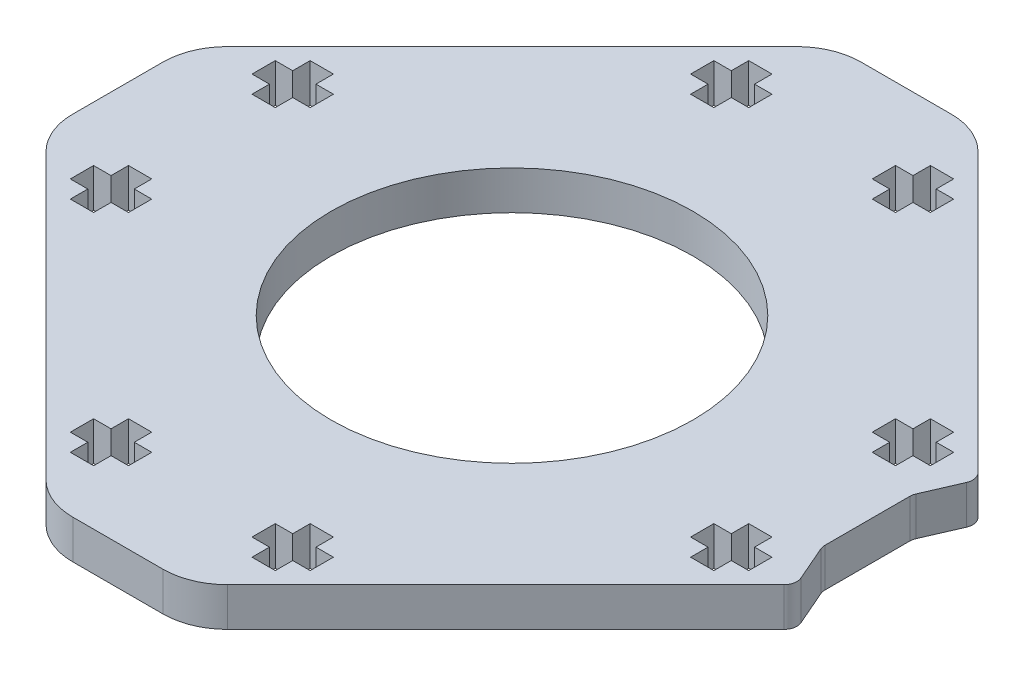
SolidWorks part; units mm, degrees
ref_plane "Front Plane" through (0, 0, 0) normal (0, 0, 1) x (1, 0, 0)
ref_plane "Top Plane" through (0, 0, 0) normal (0, 1, 0) x (1, 0, 0)
ref_plane "Right Plane" through (0, 0, 0) normal (1, 0, 0) x (0, 0, -1)
sketch "Sketch1" plane through (0, 0, 0) normal (0, 1, 0) x (1, 0, 0)
  line L0 (3.4914, 30.5) -> (-3.4914, 30.5)
  line L1 (-7.0269, 29.0355) -> (-29.0355, 7.0269)
  line L2 (-30.5, 3.4914) -> (-30.5, -3.4914)
  line L3 (-29.0355, -7.0269) -> (-7.0269, -29.0355)
  line L4 (-3.4914, -30.5) -> (3.4914, -30.5)
  line L5 (7.0269, -29.0355) -> (29.0355, -7.0269)
  line L7 (29.0355, 7.0269) -> (7.0269, 29.0355)
  line L9 (27.5, 3.4914) -> (27.5, -3.4914)
  line L11 (29.0355, 7.0269) -> (27.5, 3.4914)
  line L12 (27.5, -3.4914) -> (29.0355, -7.0269)
  arc A0 (7.0269, 29.0355) -> (3.4914, 30.5) centre (3.4914, 25.5) ccw
  arc A1 (-3.4914, 30.5) -> (-7.0269, 29.0355) centre (-3.4914, 25.5) ccw
  arc A2 (-29.0355, 7.0269) -> (-30.5, 3.4914) centre (-25.5, 3.4914) ccw
  arc A3 (-30.5, -3.4914) -> (-29.0355, -7.0269) centre (-25.5, -3.4914) ccw
  arc A4 (-7.0269, -29.0355) -> (-3.4914, -30.5) centre (-3.4914, -25.5) ccw
  arc A5 (3.4914, -30.5) -> (7.0269, -29.0355) centre (3.4914, -25.5) ccw
  circle A16 centre (0, 0) radius 14
  dimension "D1" = 28
  dimension "D2" = 31.1249
  dimension "D3" = 51
extrude "Boss-Extrude1" add sketch "Sketch1" along normal blind 3
sketch "Sketch2" plane through (0, 3, 0) normal (0, 1, 0) x (1, 0, 0)
  line L12 (-26.25, 7.9294) -> (-26.25, 6.1294)
  line L13 (-26.25, 6.1294) -> (-24.9, 6.1294)
  line L14 (-24.9, 6.1294) -> (-24.9, 4.7794)
  line L15 (-24.9, 4.7794) -> (-23.1, 4.7794)
  line L16 (-23.1, 4.7794) -> (-23.1, 6.1294)
  line L17 (-23.1, 6.1294) -> (-21.75, 6.1294)
  line L18 (-21.75, 6.1294) -> (-21.75, 7.9294)
  line L19 (-21.75, 7.9294) -> (-23.1, 7.9294)
  line L20 (-23.1, 7.9294) -> (-23.1, 9.2794)
  line L21 (-23.1, 9.2794) -> (-24.9, 9.2794)
  line L22 (-24.9, 9.2794) -> (-24.9, 7.9294)
  line L23 (-24.9, 7.9294) -> (-26.25, 7.9294)
  line L24 (-26.25, 7.9294) -> (-26.25, 6.1294)
  line L25 (-26.25, 6.1294) -> (-24.9, 6.1294)
  line L26 (-24.9, 6.1294) -> (-24.9, 4.7794)
  line L27 (-24.9, 4.7794) -> (-23.1, 4.7794)
  line L28 (-23.1, 4.7794) -> (-23.1, 6.1294)
  line L29 (-23.1, 6.1294) -> (-21.75, 6.1294)
  line L30 (-21.75, 6.1294) -> (-21.75, 7.9294)
  line L31 (-21.75, 7.9294) -> (-23.1, 7.9294)
  line L32 (-23.1, 7.9294) -> (-23.1, 9.2794)
  line L33 (-23.1, 9.2794) -> (-24.9, 9.2794)
  line L34 (-24.9, 9.2794) -> (-24.9, 7.9294)
  line L35 (-24.9, 7.9294) -> (-26.25, 7.9294)
  line L36 (-23.1, -4.7794) -> (-24.9, -4.7794)
  line L37 (-24.9, -4.7794) -> (-24.9, -6.1294)
  line L38 (-24.9, -6.1294) -> (-26.25, -6.1294)
  line L39 (-26.25, -6.1294) -> (-26.25, -7.9294)
  line L40 (-26.25, -7.9294) -> (-24.9, -7.9294)
  line L41 (-24.9, -7.9294) -> (-24.9, -9.2794)
  line L42 (-24.9, -9.2794) -> (-23.1, -9.2794)
  line L43 (-23.1, -9.2794) -> (-23.1, -7.9294)
  line L44 (-23.1, -7.9294) -> (-21.75, -7.9294)
  line L45 (-21.75, -7.9294) -> (-21.75, -6.1294)
  line L46 (-21.75, -6.1294) -> (-23.1, -6.1294)
  line L47 (-23.1, -6.1294) -> (-23.1, -4.7794)
  line L48 (-23.1, -4.7794) -> (-24.9, -4.7794)
  line L49 (-24.9, -4.7794) -> (-24.9, -6.1294)
  line L50 (-24.9, -6.1294) -> (-26.25, -6.1294)
  line L51 (-26.25, -6.1294) -> (-26.25, -7.9294)
  line L52 (-26.25, -7.9294) -> (-24.9, -7.9294)
  line L53 (-24.9, -7.9294) -> (-24.9, -9.2794)
  line L54 (-24.9, -9.2794) -> (-23.1, -9.2794)
  line L55 (-23.1, -9.2794) -> (-23.1, -7.9294)
  line L56 (-23.1, -7.9294) -> (-21.75, -7.9294)
  line L57 (-21.75, -7.9294) -> (-21.75, -6.1294)
  line L58 (-21.75, -6.1294) -> (-23.1, -6.1294)
  line L59 (-23.1, -6.1294) -> (-23.1, -4.7794)
  line L60 (7.9294, 23.1) -> (9.2794, 23.1)
  line L61 (9.2794, 23.1) -> (9.2794, 24.9)
  line L62 (9.2794, 24.9) -> (7.9294, 24.9)
  line L63 (7.9294, 24.9) -> (7.9294, 26.25)
  line L64 (7.9294, 26.25) -> (6.1294, 26.25)
  line L65 (6.1294, 26.25) -> (6.1294, 24.9)
  line L66 (6.1294, 24.9) -> (4.7794, 24.9)
  line L67 (4.7794, 24.9) -> (4.7794, 23.1)
  line L68 (4.7794, 23.1) -> (6.1294, 23.1)
  line L69 (6.1294, 23.1) -> (6.1294, 21.75)
  line L70 (6.1294, 21.75) -> (7.9294, 21.75)
  line L71 (7.9294, 21.75) -> (7.9294, 23.1)
  line L72 (7.9294, 23.1) -> (9.2794, 23.1)
  line L73 (9.2794, 23.1) -> (9.2794, 24.9)
  line L74 (9.2794, 24.9) -> (7.9294, 24.9)
  line L75 (7.9294, 24.9) -> (7.9294, 26.25)
  line L76 (7.9294, 26.25) -> (6.1294, 26.25)
  line L77 (6.1294, 26.25) -> (6.1294, 24.9)
  line L78 (6.1294, 24.9) -> (4.7794, 24.9)
  line L79 (4.7794, 24.9) -> (4.7794, 23.1)
  line L80 (4.7794, 23.1) -> (6.1294, 23.1)
  line L81 (6.1294, 23.1) -> (6.1294, 21.75)
  line L82 (6.1294, 21.75) -> (7.9294, 21.75)
  line L83 (7.9294, 21.75) -> (7.9294, 23.1)
  line L84 (26.25, -7.9294) -> (26.25, -6.1294)
  line L85 (26.25, -6.1294) -> (24.9, -6.1294)
  line L86 (24.9, -6.1294) -> (24.9, -4.7794)
  line L87 (24.9, -4.7794) -> (23.1, -4.7794)
  line L88 (23.1, -4.7794) -> (23.1, -6.1294)
  line L89 (23.1, -6.1294) -> (21.75, -6.1294)
  line L90 (21.75, -6.1294) -> (21.75, -7.9294)
  line L91 (21.75, -7.9294) -> (23.1, -7.9294)
  line L92 (23.1, -7.9294) -> (23.1, -9.2794)
  line L93 (23.1, -9.2794) -> (24.9, -9.2794)
  line L94 (24.9, -9.2794) -> (24.9, -7.9294)
  line L95 (24.9, -7.9294) -> (26.25, -7.9294)
  line L96 (26.25, -7.9294) -> (26.25, -6.1294)
  line L97 (26.25, -6.1294) -> (24.9, -6.1294)
  line L98 (24.9, -6.1294) -> (24.9, -4.7794)
  line L99 (24.9, -4.7794) -> (23.1, -4.7794)
  line L100 (23.1, -4.7794) -> (23.1, -6.1294)
  line L101 (23.1, -6.1294) -> (21.75, -6.1294)
  line L102 (21.75, -6.1294) -> (21.75, -7.9294)
  line L103 (21.75, -7.9294) -> (23.1, -7.9294)
  line L104 (23.1, -7.9294) -> (23.1, -9.2794)
  line L105 (23.1, -9.2794) -> (24.9, -9.2794)
  line L106 (24.9, -9.2794) -> (24.9, -7.9294)
  line L107 (24.9, -7.9294) -> (26.25, -7.9294)
  line L108 (-4.7794, 24.9) -> (-6.1294, 24.9)
  line L109 (-6.1294, 24.9) -> (-6.1294, 26.25)
  line L110 (-6.1294, 26.25) -> (-7.9294, 26.25)
  line L111 (-7.9294, 26.25) -> (-7.9294, 24.9)
  line L112 (-7.9294, 24.9) -> (-9.2794, 24.9)
  line L113 (-9.2794, 24.9) -> (-9.2794, 23.1)
  line L114 (-9.2794, 23.1) -> (-7.9294, 23.1)
  line L115 (-7.9294, 23.1) -> (-7.9294, 21.75)
  line L116 (-7.9294, 21.75) -> (-6.1294, 21.75)
  line L117 (-6.1294, 21.75) -> (-6.1294, 23.1)
  line L118 (-6.1294, 23.1) -> (-4.7794, 23.1)
  line L119 (-4.7794, 23.1) -> (-4.7794, 24.9)
  line L120 (-4.7794, 24.9) -> (-6.1294, 24.9)
  line L121 (-6.1294, 24.9) -> (-6.1294, 26.25)
  line L122 (-6.1294, 26.25) -> (-7.9294, 26.25)
  line L123 (-7.9294, 26.25) -> (-7.9294, 24.9)
  line L124 (-7.9294, 24.9) -> (-9.2794, 24.9)
  line L125 (-9.2794, 24.9) -> (-9.2794, 23.1)
  line L126 (-9.2794, 23.1) -> (-7.9294, 23.1)
  line L127 (-7.9294, 23.1) -> (-7.9294, 21.75)
  line L128 (-7.9294, 21.75) -> (-6.1294, 21.75)
  line L129 (-6.1294, 21.75) -> (-6.1294, 23.1)
  line L130 (-6.1294, 23.1) -> (-4.7794, 23.1)
  line L131 (-4.7794, 23.1) -> (-4.7794, 24.9)
  line L132 (26.25, 7.9294) -> (24.9, 7.9294)
  line L133 (26.25, 6.1294) -> (26.25, 7.9294)
  line L134 (24.9, 6.1294) -> (26.25, 6.1294)
  line L135 (24.9, 4.7794) -> (24.9, 6.1294)
  line L136 (23.1, 4.7794) -> (24.9, 4.7794)
  line L137 (23.1, 6.1294) -> (23.1, 4.7794)
  line L138 (21.75, 6.1294) -> (23.1, 6.1294)
  line L139 (21.75, 7.9294) -> (21.75, 6.1294)
  line L140 (23.1, 7.9294) -> (21.75, 7.9294)
  line L141 (23.1, 9.2794) -> (23.1, 7.9294)
  line L142 (24.9, 9.2794) -> (23.1, 9.2794)
  line L143 (24.9, 7.9294) -> (24.9, 9.2794)
  line L144 (26.25, 7.9294) -> (24.9, 7.9294)
  line L145 (26.25, 6.1294) -> (26.25, 7.9294)
  line L146 (24.9, 6.1294) -> (26.25, 6.1294)
  line L147 (24.9, 4.7794) -> (24.9, 6.1294)
  line L148 (23.1, 4.7794) -> (24.9, 4.7794)
  line L149 (23.1, 6.1294) -> (23.1, 4.7794)
  line L150 (21.75, 6.1294) -> (23.1, 6.1294)
  line L151 (21.75, 7.9294) -> (21.75, 6.1294)
  line L152 (23.1, 7.9294) -> (21.75, 7.9294)
  line L153 (23.1, 9.2794) -> (23.1, 7.9294)
  line L154 (24.9, 9.2794) -> (23.1, 9.2794)
  line L155 (24.9, 7.9294) -> (24.9, 9.2794)
  line L156 (-6.1294, -26.25) -> (-6.1294, -24.9)
  line L157 (-6.1294, -24.9) -> (-4.7794, -24.9)
  line L158 (-4.7794, -24.9) -> (-4.7794, -23.1)
  line L159 (-4.7794, -23.1) -> (-6.1294, -23.1)
  line L160 (-6.1294, -23.1) -> (-6.1294, -21.75)
  line L161 (-6.1294, -21.75) -> (-7.9294, -21.75)
  line L162 (-7.9294, -21.75) -> (-7.9294, -23.1)
  line L163 (-7.9294, -23.1) -> (-9.2794, -23.1)
  line L164 (-9.2794, -23.1) -> (-9.2794, -24.9)
  line L165 (-9.2794, -24.9) -> (-7.9294, -24.9)
  line L166 (-7.9294, -24.9) -> (-7.9294, -26.25)
  line L167 (-7.9294, -26.25) -> (-6.1294, -26.25)
  line L168 (-6.1294, -26.25) -> (-6.1294, -24.9)
  line L169 (-6.1294, -24.9) -> (-4.7794, -24.9)
  line L170 (-4.7794, -24.9) -> (-4.7794, -23.1)
  line L171 (-4.7794, -23.1) -> (-6.1294, -23.1)
  line L172 (-6.1294, -23.1) -> (-6.1294, -21.75)
  line L173 (-6.1294, -21.75) -> (-7.9294, -21.75)
  line L174 (-7.9294, -21.75) -> (-7.9294, -23.1)
  line L175 (-7.9294, -23.1) -> (-9.2794, -23.1)
  line L176 (-9.2794, -23.1) -> (-9.2794, -24.9)
  line L177 (-9.2794, -24.9) -> (-7.9294, -24.9)
  line L178 (-7.9294, -24.9) -> (-7.9294, -26.25)
  line L179 (-7.9294, -26.25) -> (-6.1294, -26.25)
  line L180 (7.9294, -26.25) -> (7.9294, -24.9)
  line L181 (7.9294, -24.9) -> (9.2794, -24.9)
  line L182 (9.2794, -24.9) -> (9.2794, -23.1)
  line L183 (9.2794, -23.1) -> (7.9294, -23.1)
  line L184 (7.9294, -23.1) -> (7.9294, -21.75)
  line L185 (7.9294, -21.75) -> (6.1294, -21.75)
  line L186 (6.1294, -21.75) -> (6.1294, -23.1)
  line L187 (6.1294, -23.1) -> (4.7794, -23.1)
  line L188 (4.7794, -23.1) -> (4.7794, -24.9)
  line L189 (4.7794, -24.9) -> (6.1294, -24.9)
  line L190 (6.1294, -24.9) -> (6.1294, -26.25)
  line L191 (6.1294, -26.25) -> (7.9294, -26.25)
  line L192 (7.9294, -26.25) -> (7.9294, -24.9)
  line L193 (7.9294, -24.9) -> (9.2794, -24.9)
  line L194 (9.2794, -24.9) -> (9.2794, -23.1)
  line L195 (9.2794, -23.1) -> (7.9294, -23.1)
  line L196 (7.9294, -23.1) -> (7.9294, -21.75)
  line L197 (7.9294, -21.75) -> (6.1294, -21.75)
  line L198 (6.1294, -21.75) -> (6.1294, -23.1)
  line L199 (6.1294, -23.1) -> (4.7794, -23.1)
  line L200 (4.7794, -23.1) -> (4.7794, -24.9)
  line L201 (4.7794, -24.9) -> (6.1294, -24.9)
  line L202 (6.1294, -24.9) -> (6.1294, -26.25)
  line L203 (6.1294, -26.25) -> (7.9294, -26.25)
  dimension "D1" = 0
  dimension "D2" = 0
  dimension "D3" = 0
  dimension "D4" = 0
  dimension "D5" = 0
  dimension "D6" = 0
  dimension "D7" = 0
  dimension "D8" = 0
extrude "Cut-Extrude1" cut sketch "Sketch2" against normal through all
fillet "Fillet1" radius 1 4 edges at (29.0355, 1.5, 7.0269) (27.5, 1.5, 3.4914) (27.5, 1.5, -3.4914) (29.0355, 1.5, -7.0269)
